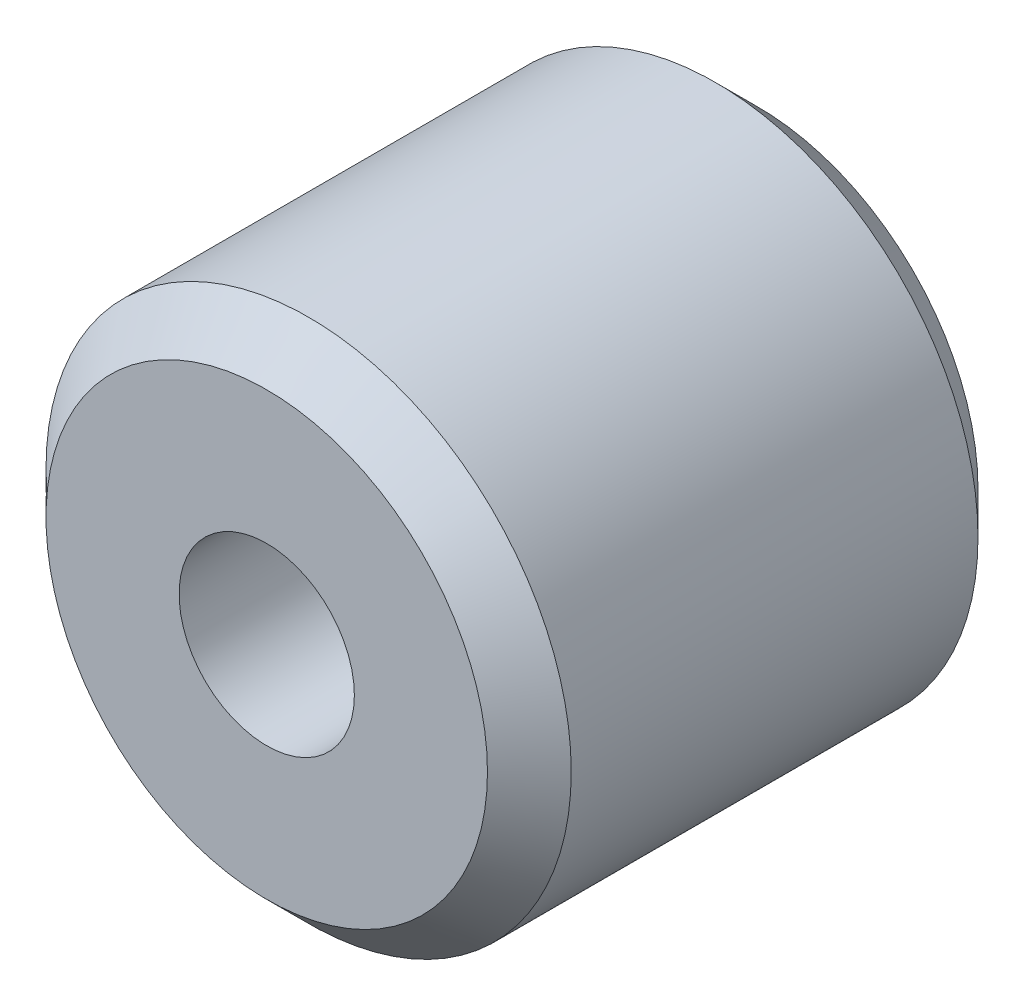
SolidWorks part; units mm, degrees
ref_plane "Front Plane" through (0, 0, 0) normal (0, 0, 1) x (1, 0, 0)
ref_plane "Top Plane" through (0, 0, 0) normal (0, 1, 0) x (1, 0, 0)
ref_plane "Right Plane" through (0, 0, 0) normal (1, 0, 0) x (0, 0, -1)
sketch "Sketch1" plane through (0, 0, 0) normal (0, 0, 1) x (1, 0, 0)
  circle A0 centre (0, 0) radius 4.765
  circle A1 centre (0, 0) radius 1.59
  dimension "D1" = 9.53
  dimension "D2" = 3.18
extrude "Boss-Extrude1" add sketch "Sketch1" along normal mid plane 8.9
chamfer "Chamfer1" distance 0.76 angle 45 2 edges at (4.765, 0, -4.45) (4.765, 0, 4.45)
